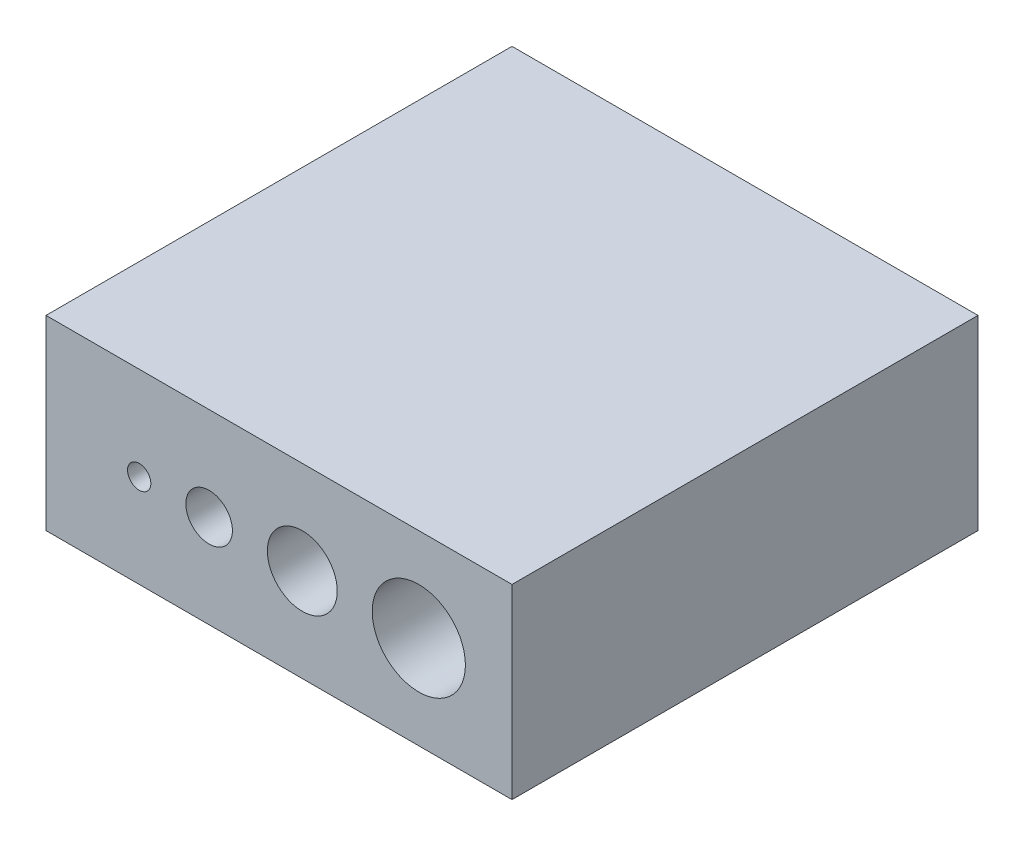
SolidWorks part; units mm, degrees
ref_plane "Front Plane" through (0, 0, 0) normal (0, 0, 1) x (1, 0, 0)
ref_plane "Top Plane" through (0, 0, 0) normal (0, 1, 0) x (1, 0, 0)
ref_plane "Right Plane" through (0, 0, 0) normal (1, 0, 0) x (0, 0, -1)
sketch "Sketch1" plane through (0, 0, 0) normal (0, 0, 1) x (1, 0, 0)
  line L1 (0, 0) -> (20, 0)
  line L2 (0, 0) -> (0, 8)
  line L3 (0, 8) -> (20, 8)
  line L4 (20, 0) -> (20, 8)
  dimension "D1" = 20
  dimension "D2" = 8
extrude "Boss-Extrude1" add sketch "Sketch1" against normal blind 20
sketch "Sketch2" plane through (0, 0, 0) normal (0, 0, 1) x (1, 0, 0)
  line L0 (0, 8) -> (0, 0) construction
  line L2 (0, 0) -> (20, 0) construction
  circle A0 centre (4, 4) radius 0.5
  circle A1 centre (7, 4) radius 1
  circle A2 centre (11, 4) radius 1.5
  circle A3 centre (16, 4) radius 2
  point P10 (-6.3949, 11.7491)
  point P13 (3.5291, 0)
  dimension "D1" = 1
  dimension "D2" = 3
  dimension "D3" = 4
  dimension "D4" = 4
  dimension "D5" = 5
  dimension "D6" = 4
extrude "Cut-Extrude1" cut sketch "Sketch2" against normal through all
